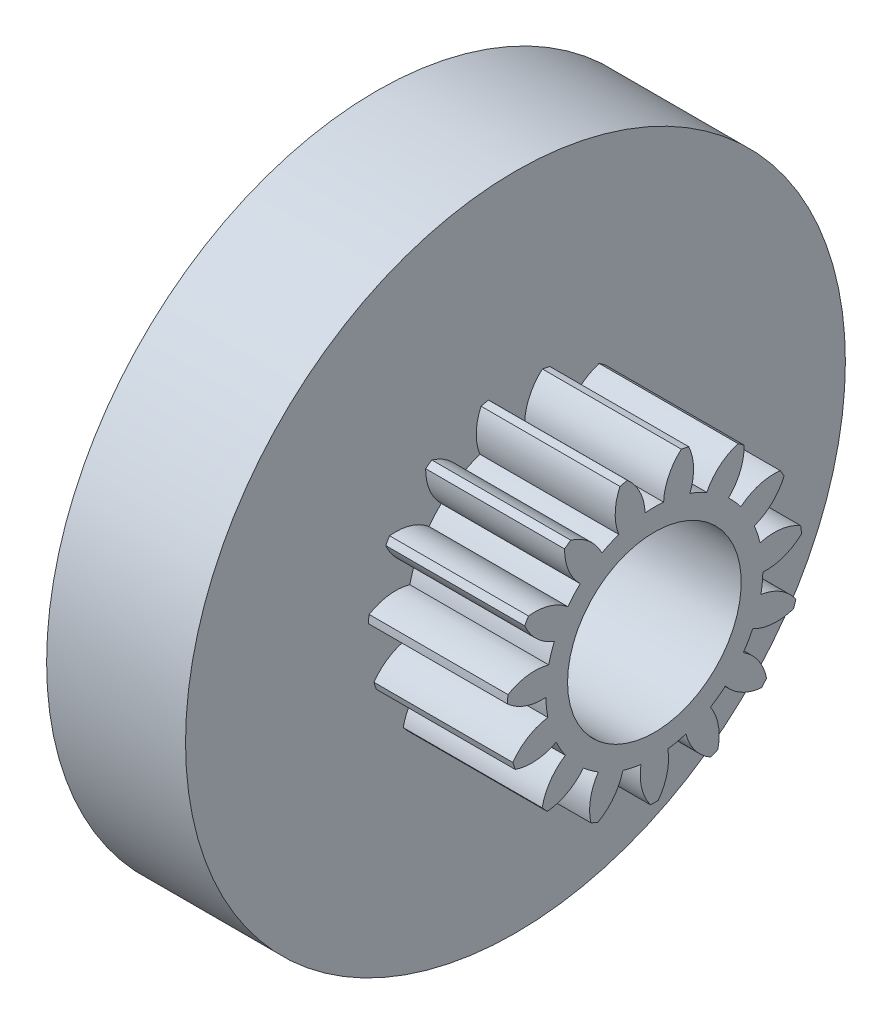
SolidWorks part; units mm, degrees
ref_plane "Plane1" through (0, 0, 0) normal (0, 0, 1) x (1, 0, 0)
ref_plane "Plane2" through (0, 0, 0) normal (0, 1, 0) x (1, 0, 0)
ref_plane "Plane3" through (0, 0, 0) normal (1, 0, 0) x (0, 0, -1)
sketch "HoldingSke" plane through (0, 0, 0) normal (0, 1, 0) x (1, 0, 0)
  line L0 (0, 0) -> (1.9319, -0.5176)
  line L1 (-15, 0) -> (100, 0) construction
  line L2 (0, 0) -> (-2.1039, 2.3779)
  line L3 (0, 0) -> (-11.863, 4.5341)
  line L4 (0, 0) -> (8.3417, 2.2352)
  line L5 (0, 0) -> (-7.4956, -2.7956)
  line L6 (0, 0) -> (-3.3159, -2.2372)
  line L7 (-2.1039, 2.3779) -> (-0.3819, 10.1904)
  line L8 (-76.2, 54.61) -> (-75.3, 54.61)
  line L9 (-71.009, 38.7566) -> (-53.1078, 45.2721)
  line L10 (-76.2, 71.12) -> (104.1128, 71.12)
  line L11 (0, 0) -> (-4, 0)
  line L12 (-76.2, 101.6) -> (-76.181, 101.6)
  line L13 (24.9733, 27.94) -> (52.9518, 28.4284)
  line L14 (24.9733, 27.94) -> (24.9743, 27.94)
  line L15 (24.9733, 27.94) -> (100.4006, 29.5858)
  line L16 (-63.627, -0.5) -> (-12.827, -0.5)
  circle A0 centre (0, 0) radius 2.5
  circle A1 centre (0, 0) radius 3.124
  circle A2 centre (0, 0) radius 10
  circle A3 centre (0, 0) radius 2.5
  dimension "MHD" = 6.248
  dimension "Hub_dia" = 20
  dimension "Bore" = 5
  dimension "MBD" = 5
  dimension "Num_teeth" = 15
  dimension "Pitch_radius" = 180.3128
  dimension "Pitch" = 2
  dimension "Width" = 4
  dimension "Overall_len" = 8
  dimension "Show_teeth" = 15
  dimension "Thickness" = 4
  dimension "OAL" = 8.0001
  dimension "T_dim" = 0.9
  dimension "Ap" = 20
  dimension "H" = 19.05
  dimension "Backlash" = 0.019
  dimension "Addendum_fac" = 1
  dimension "Dedendum_fac" = 1.25
  dimension "Clearance_fac" = 0.25
  dimension "Dedendum_add" = 0.001
  dimension "Module" = 0.5
sketch "BasProSke" plane through (0, 0, 0) normal (0, 1, 0) x (1, 0, 0)
  line L0 (-10, 0) -> (60, 0) construction
  line L1 (0, 0) -> (0, 4.25)
  line L2 (0, 0) -> (4, 0)
  line L3 (4, 0) -> (4, 4.25)
  line L4 (4, 4.25) -> (0, 4.25)
  dimension "Diameter" = 8.5
  dimension "Thickness" = 4
revolve "Base-Revolve" add sketch "BasProSke" angle 360 about L0
sketch "TooCutSke" plane through (0, 0, 0) normal (1, 0, 0) x (0, 0, -1)
  line L1 (0, 0) -> (0, 107) construction
  line L2 (0, 0) -> (-0.4252, 3.7258) construction
  line L3 (0, 0) -> (-1.5522, 7.3025) construction
  line L4 (-0.4252, 3.7258) -> (-0.7761, 3.6512) construction
  arc A0 (0.2658, 3.1127) -> (-0.2658, 3.1127) centre (0, 0) ccw
  arc A1 (0.8008, 4.1997) -> (-0.8008, 4.1997) centre (0, 0) ccw
  circle A2 centre (0, 0) radius 3.75 construction
  circle A3 centre (0, 0) radius 3.5238 construction
  arc A4 (-0.2658, 3.1127) -> (-0.8008, 4.1997) centre (-1.7645, 3.0503) ccw
  arc A5 (0.8008, 4.1997) -> (0.2658, 3.1127) centre (1.7645, 3.0503) ccw
  dimension "Root_dia" = 6.248
  dimension "Overcut_dia" = 8.5508
  dimension "Pitch_dia" = 7.5
  dimension "Base_dia" = 7.0477
  dimension "Flank_rad" = 1.5
  dimension "Half_ang" = 12
  dimension "Half_CT" = 0.3587
extrude "ToothCut" cut sketch "TooCutSke" along normal through all
fillet "Breaks" [suppressed] radius 0.01
fillet "RootFillets" [suppressed] radius 0.126
pattern_circular "TeethCuts" count 15 every 24 about axis through (-10, 0, 0) along (1, 0, 0) of "ToothCut", "RootFillets", "Breaks"
sketch "HubNeaOneSke" plane through (0, 0, 0) normal (-1, 0, 0) x (0, 0, 1)
  circle A0 centre (0, 0) radius 9.5
extrude "HubNearOne" add sketch "HubNeaOneSke" along normal blind 4.0001
ref_plane "FarPln" through (4, 0, 0) normal (1, 0, 0) x (0, 0, -1)
sketch "HubFarSke" plane through (4, 0, 0) normal (1, 0, 0) x (0, 0, -1)
  circle A0 centre (0, 0) radius 3.124
  dimension "Diameter" = 6.248
extrude "HubFar" [suppressed] add sketch "HubFarSke" along normal blind 2.0001
sketch "BorSke" plane through (0, 0, 0) normal (1, 0, 0) x (0, 0, -1)
  circle A0 centre (0, 0) radius 2.5
  dimension "Diameter" = 5
extrude "Bore" cut sketch "BorSke" along normal mid plane 16.0002
sketch "KeySke" plane through (0, 0, 0) normal (1, 0, 0) x (0, 0, -1)
  line L0 (-1, 0) -> (-1, 3.4)
  line L1 (-1, 3.4) -> (1, 3.4)
  line L2 (1, 3.4) -> (1, 0)
  line L3 (0, 0) -> (0, 34) construction
  line L4 (-1, 0) -> (1, 0)
  dimension "Offset" = 3.4
  dimension "Width" = 2
extrude "Keyway" [suppressed] cut sketch "KeySke" along normal mid plane 16.0002
pattern_circular "Keyway2" [suppressed] count 2 every 90 about axis through (-10, 0, 0) along (1, 0, 0)
